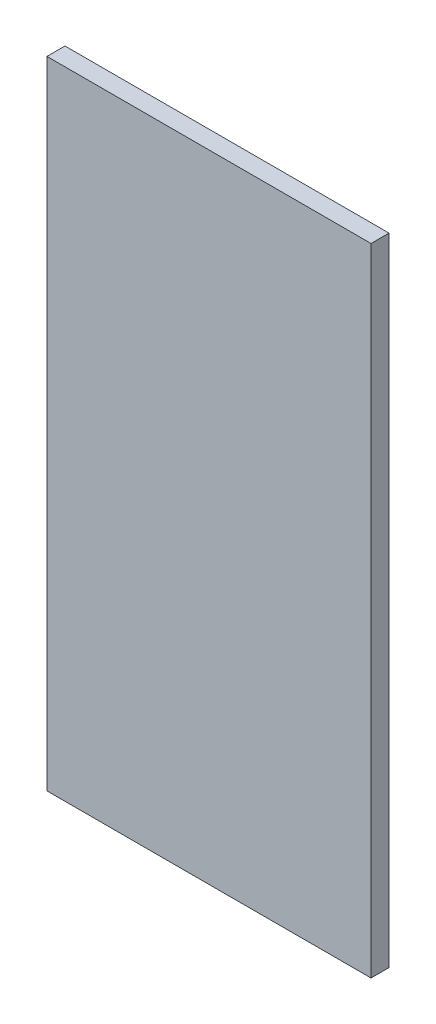
SolidWorks part; units mm, degrees
material "Balsa"
ref_plane "Front Plane" through (0, 0, 0) normal (0, 0, 1) x (1, 0, 0)
ref_plane "Top Plane" through (0, 0, 0) normal (0, 1, 0) x (1, 0, 0)
ref_plane "Right Plane" through (0, 0, 0) normal (1, 0, 0) x (0, 0, -1)
sketch "Sketch1" plane through (0, 0, 0) normal (0, 0, 1) x (1, 0, 0)
  line L1 (0, 0) -> (270, 0)
  line L2 (0, 0) -> (0, 530)
  line L3 (0, 530) -> (270, 530)
  line L4 (270, 0) -> (270, 530)
  dimension "D1" = 270
  dimension "D2" = 530
extrude "Boss-Extrude1" add sketch "Sketch1" along normal blind 15
